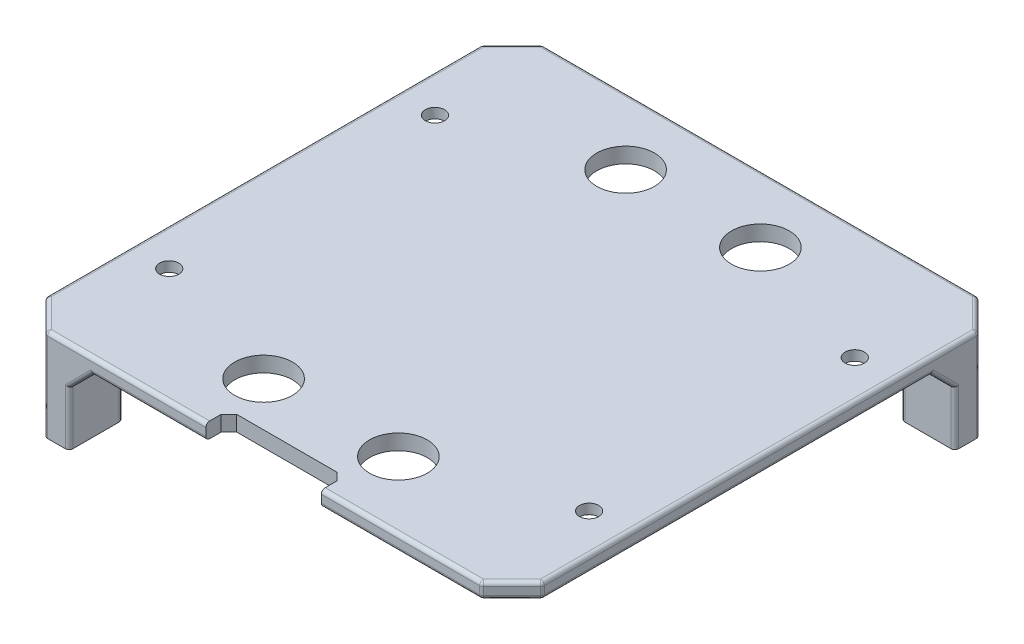
SolidWorks part; units mm, degrees
ref_plane "Front Plane" through (0, 0, 0) normal (0, 0, 1) x (1, 0, 0)
ref_plane "Top Plane" through (0, 0, 0) normal (0, 1, 0) x (1, 0, 0)
ref_plane "Right Plane" through (0, 0, 0) normal (1, 0, 0) x (0, 0, -1)
sketch "Sketch2" plane through (0, 0, 0) normal (0, 1, 0) x (1, 0, 0)
  line L1 (-32.25, -32.25) -> (32.25, -32.25)
  line L2 (-32.25, -32.25) -> (-32.25, 32.25)
  line L3 (-32.25, 32.25) -> (32.25, 32.25)
  line L4 (32.25, -32.25) -> (32.25, 32.25)
  line L5 (-32.25, -32.25) -> (32.25, 32.25) construction
  line L6 (-32.25, 32.25) -> (32.25, -32.25) construction
  point P0 (0, 0)
  dimension "D1" = 64.5
extrude "Boss-Extrude1" add sketch "Sketch2" along normal blind 2
sketch "Sketch3" plane through (0, 0, 0) normal (0, -1, 0) x (1, 0, 0)
  line L1 (-32.25, 32.25) -> (-25.25, 32.25)
  line L2 (-32.25, 32.25) -> (-32.25, 25.25)
  line L3 (-32.25, 25.25) -> (-25.25, 25.25)
  line L4 (-25.25, 32.25) -> (-25.25, 25.25)
  line L6 (-32.25, 32.25) -> (32.25, 32.25) construction
  line L7 (-32.25, -32.25) -> (-32.25, 32.25) construction
  dimension "D1" = 7
extrude "Boss-Extrude2" add sketch "Sketch3" along normal blind 10
sketch "Sketch6" plane through (0, -10, 0) normal (0, -1, 0) x (1, 0, 0)
  line L0 (-32.25, 32.25) -> (-25.25, 25.25) construction
  line L1 (-32.25, 25.25) -> (-25.25, 32.25) construction
  circle A0 centre (-28.75, 28.75) radius 1
  point P8 (-28.75, 28.75)
  dimension "D1" = 2
extrude "Cut-Extrude2" cut sketch "Sketch6" against normal blind 3
sketch "Sketch7" plane through (0, 0, 0) normal (0, 0, 1) x (1, 0, 0)
  line L0 (0, 0) -> (0, 2) construction
  line L1 (-32.25, 2) -> (32.25, 2) construction
fillet "Fillet3" [suppressed] radius 5
chamfer "Chamfer3" distance 3 angle 45 2 edges at (-25.25, 0, 28.75) (-28.75, 0, 25.25)
pattern_circular "CirPattern1" count 3 every 90 about axis through (0, 0, 0) along (0, 1, 0) of "Cut-Extrude2", "Boss-Extrude2", "Chamfer3"
sketch "Sketch8" plane through (0, 2, 0) normal (0, 1, 0) x (1, 0, 0)
  line L0 (32.25, -23) -> (-32.25, -23) construction
  line L1 (32.25, -32.25) -> (32.25, 32.25) construction
  line L2 (-32.25, 32.25) -> (-32.25, -32.25) construction
  line L3 (32.25, 23) -> (-32.25, 23) construction
  line L4 (10, 23) -> (10, -23) construction
  line L5 (-10, -23) -> (-10, 23) construction
  line L6 (10, 0) -> (-10, 0) construction
  line L7 (26, -23) -> (10, 23) construction
  line L8 (10, -23) -> (26, -23) construction
  line L9 (10, -23) -> (10, 23) construction
  line L10 (10, 23) -> (26, 23) construction
  line L11 (26, -23) -> (26, 23) construction
  line L12 (26, 23) -> (10, -23) construction
  line L13 (9, -24) -> (9, -27)
  line L14 (30, 27) -> (6, 27)
  line L15 (30, 27) -> (30, -27)
  line L16 (30, -27) -> (6, -27)
  line L17 (6, 27) -> (6, -27)
  line L18 (30, 27) -> (6, -27) construction
  line L19 (30, -27) -> (6, 27) construction
  line L20 (27, 24) -> (9, 24)
  line L21 (27, 24) -> (27, -24)
  line L22 (27, -24) -> (9, -24)
  line L23 (9, 24) -> (9, -24)
  line L24 (27, 24) -> (9, -24) construction
  line L25 (27, -24) -> (9, 24) construction
  line L26 (9, 24) -> (9, 27)
  line L27 (26, 23) -> (30, 23)
  line L28 (26, 23) -> (26, 27)
  line L29 (26, -23) -> (26, -27)
  line L30 (26, -23) -> (30, -23)
  point P14 (0, 0)
  point P18 (18, 0)
  point P23 (18, 0)
  dimension "D1" = 20
  dimension "D2" = 46
  dimension "D3" = 16
  dimension "D4" = 1
  dimension "D5" = 1
  dimension "D6" = 3
  dimension "D7" = 3
extrude "Boss-Extrude3" [suppressed] add sketch "Sketch8" along normal blind 10.2 contours L20 L28 L14 L26 | L21 L30 L15 L27 | L29 L22 L13 L16
sketch "Sketch9" [suppressed] plane through (27, 0, 0) normal (-1, 0, 0) x (0, 0, 1)
  line L0 (23, 12.2) -> (23, 2) construction
  line L1 (-23, 12.2) -> (23, 12.2)
  line L2 (-23, 12.2) -> (-23, 11.2)
  line L3 (-23, 11.2) -> (23, 11.2)
  line L4 (23, 12.2) -> (23, 11.2)
  dimension "D1" = 1
extrude "Boss-Extrude4" [suppressed] add sketch "Sketch9" along normal blind 1
sketch "Sketch11" [suppressed] plane through (0, 0, 24) normal (0, 0, -1) x (-1, 0, 0)
  line L0 (-9, 12.2) -> (-9, 2) construction
  line L1 (-26, 12.2) -> (-9, 12.2)
  line L2 (-26, 12.2) -> (-26, 11.2)
  line L3 (-26, 11.2) -> (-9, 11.2)
  line L4 (-9, 12.2) -> (-9, 11.2)
  dimension "D1" = 1
extrude "Boss-Extrude8" [suppressed] add sketch "Sketch11" along normal blind 1 separate body
chamfer "Chamfer1" [suppressed] distance 0.5 angle 45
fillet "Fillet1" [suppressed] radius 0.25
chamfer "Chamfer2" [suppressed] distance 0.5 angle 45
fillet "Fillet2" [suppressed] radius 0.25
mirror "Mirror2" [suppressed] about plane through (0, 0, 0) normal (0, 0, 1)
mirror "Mirror3" [suppressed] about plane through (0, 0, 0) normal (1, 0, 0)
mirror "Mirror4" [suppressed] about plane through (0, 0, 0) normal (1, 0, 0)
sketch "Sketch15" plane through (0, 2, 0) normal (0, 1, 0) x (1, 0, 0)
  line L0 (0, 32.25) -> (0, -32.25) construction
  line L1 (32.25, 32.25) -> (-32.25, 32.25) construction
  line L2 (-32.25, -32.25) -> (32.25, -32.25) construction
  line L3 (-18, 32.25) -> (-18, -32.25) construction
  line L4 (-32.25, 0) -> (32.25, 0) construction
  line L5 (-32.25, 32.25) -> (-32.25, -32.25) construction
  line L6 (32.25, -32.25) -> (32.25, 32.25) construction
  line L7 (-32.25, 20.25) -> (32.25, 20.25) construction
  circle A0 centre (-18, 20.25) radius 1.25
  circle A1 centre (18, 20.25) radius 1.25
  circle A2 centre (18, -20.25) radius 1.25
  circle A3 centre (-18, -20.25) radius 1.25
  dimension "D3" = 2.5
  dimension "D1" = 18
  dimension "D2" = 12
extrude "Cut-Extrude5" [suppressed] cut sketch "Sketch15" against normal blind 10
chamfer "Chamfer8" distance 4 angle 45 4 edges at (32.25, -4, -32.25) (-32.25, -4, -32.25) (-32.25, -4, 32.25) (32.25, 1, 32.25)
fillet "Fillet4" radius 0.5 36 edges at (30.25, 0, 30.25) (0, 2, 32.25) (-28.25, -4, 32.25) (28.25, 1, 32.25) (0, 2, -32.25) (-32.25, 2, 0) (-30.25, 2, 30.25) (-30.25, 2, -30.25) (30.25, 2, -30.25) (30.25, 2, 30.25) (-28.25, -4, -32.25) (28.25, -4, -32.25) (-32.25, -4, 28.25) (-32.25, -4, -28.25) (-32.25, -6.5, 25.25) (-25.25, -6.5, 25.25) (-25.25, -6.5, 32.25) (3, 0, 32.25) (-23.75, -1.5, 32.25) (-32.25, -1.5, 23.75) (-25.25, -6.5, -32.25) (-25.25, -6.5, -25.25) (-32.25, -6.5, -25.25) (32.25, -6.5, -25.25) (25.25, -6.5, -25.25) (25.25, -6.5, -32.25) (-32.25, 0, 0) (-32.25, -1.5, -23.75) (-23.75, -1.5, -32.25) (0, 0, -32.25) (23.75, -1.5, -32.25) (32.25, -1.5, -23.75) (32.25, 0, 3) (32.25, 2, 0) (32.25, -4, -28.25) (32.25, 1, 28.25)
sketch "Sketch12" plane through (0, 2, 0) normal (0, 1, 0) x (1, 0, 0)
  line L0 (0, -32.25) -> (0, 32.25) construction
  line L1 (28.0429, -32.25) -> (-28.0429, -32.25) construction
  line L2 (-28.0429, 32.25) -> (28.0429, 32.25) construction
  line L4 (7.5, -29.25) -> (-7.5, -29.25)
  line L5 (7.5, -29.25) -> (7.5, -32.25)
  line L6 (7.5, -32.25) -> (-7.5, -32.25)
  line L7 (-7.5, -29.25) -> (-7.5, -32.25)
  line L8 (7.5, -29.25) -> (-7.5, -32.25) construction
  line L9 (7.5, -32.25) -> (-7.5, -29.25) construction
  point P6 (0, -30.75)
  dimension "D1" = 15
  dimension "D2" = 3
extrude "Cut-Extrude3" cut sketch "Sketch12" against normal blind 10
chamfer "Chamfer9" distance 1 angle 45 2 edges at (-7.5, 1, 29.25) (7.5, 1, 29.25)
sketch "Sketch13" plane through (0, 2, 0) normal (0, 1, 0) x (1, 0, 0)
  line L0 (0, -29.25) -> (0, 32.25) construction
  line L1 (6.5, -29.25) -> (-6.5, -29.25) construction
  line L2 (-28.0429, 32.25) -> (28.0429, 32.25) construction
  line L3 (5, -31.75) -> (5, 32.25) construction
  line L4 (7.5, -31.75) -> (28.0429, -31.75) construction
  line L5 (32.25, -27.25) -> (-32.25, -27.25) construction
  line L6 (32.25, 28.0429) -> (32.25, -28.0429) construction
  line L7 (-32.25, -28.0429) -> (-32.25, 28.0429) construction
  line L8 (32.25, 0) -> (-32.25, 0) construction
  line L9 (28.0429, -32.25) -> (7.5, -32.25) construction
  circle A0 centre (8.75, -23.5) radius 3.75
  circle A1 centre (-8.75, -23.5) radius 3.75
  circle A2 centre (-8.75, 23.5) radius 3.75
  circle A3 centre (8.75, 23.5) radius 3.75
  dimension "D2" = 7.5
  dimension "D1" = 5
  dimension "D3" = 5
extrude "Cut-Extrude4" cut sketch "Sketch13" against normal blind 10
sketch "Sketch16" plane through (0, 0, 0) normal (0, -1, 0) x (1, 0, 0)
  line L0 (0, -32.25) -> (0, 32.25) construction
  line L1 (22.4571, -32.25) -> (-22.4571, -32.25) construction
  line L2 (-7.5, 32.25) -> (7.5, 32.25) construction
  line L3 (-32.25, 0) -> (32.25, 0) construction
  line L4 (-32.25, -22.4571) -> (-32.25, 22.4571) construction
  line L5 (32.25, 28.0429) -> (32.25, -22.4571) construction
  line L6 (-27.25, -32.25) -> (-27.25, 32.25) construction
  line L7 (-22.4571, 32.25) -> (-7.5, 32.25) construction
  line L8 (-32.25, -17.25) -> (32.25, -17.25) construction
  circle A0 centre (-27.25, -17.25) radius 1.25
  circle A1 centre (-27.25, 17.25) radius 1.25
  circle A2 centre (27.25, -17.25) radius 1.25
  circle A3 centre (27.25, 17.25) radius 1.25
  dimension "D3" = 2.5
  dimension "D1" = 5
  dimension "D2" = 15
extrude "Cut-Extrude6" cut sketch "Sketch16" against normal blind 10
chamfer "Chamfer10" distance 1 angle 35 4 edges at (-27.25, 0, -18.5) (-27.25, 0, 18.5) (27.25, 0, 16) (27.25, 0, -16)
